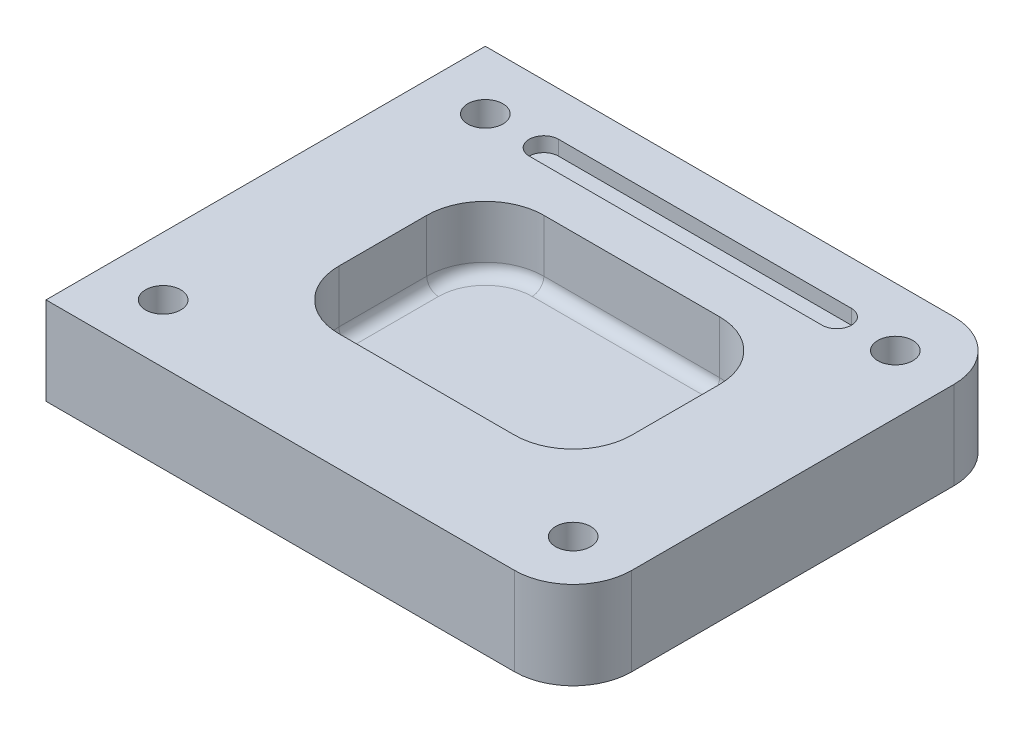
SolidWorks part; units mm, degrees
ref_plane "Front Plane" through (0, 0, 0) normal (0, 0, 1) x (1, 0, 0)
ref_plane "Top Plane" through (0, 0, 0) normal (0, 1, 0) x (1, 0, 0)
ref_plane "Right Plane" through (0, 0, 0) normal (1, 0, 0) x (0, 0, -1)
sketch "Sketch1" plane through (0, 0, 0) normal (0, 1, 0) x (1, 0, 0)
  line L1 (-90, -75) -> (90, -75)
  line L2 (-90, -75) -> (-90, 75)
  line L3 (-90, 75) -> (90, 75)
  line L4 (90, -75) -> (90, 75)
  line L5 (-90, -75) -> (90, 75) construction
  line L6 (-90, 75) -> (90, -75) construction
  point P0 (0, 0)
  dimension "D1" = 180
  dimension "D2" = 150
extrude "Boss-Extrude1" add sketch "Sketch1" along normal blind 30
sketch "Sketch2" plane through (0, 30, 0) normal (0, 1, 0) x (1, 0, 0)
  line L8 (70, -55) -> (70, 55)
  line L9 (70, 55) -> (-70, 55)
  line L10 (-70, 55) -> (-70, -55)
  line L11 (-70, -55) -> (70, -55)
  line L12 (70, -55) -> (70, 55) construction
  line L13 (70, 55) -> (-70, 55) construction
  line L14 (-70, 55) -> (-70, -55) construction
  line L15 (-70, -55) -> (70, -55) construction
  dimension "D1" = 20
hole_wizard "Ø16.0mm Dowel Hole1" positions "3DSketch2" profile "Sketch4" hole size "Ø16.0" standard "ANSI Metric"
sketch3d "3DSketch2"
  point P0 (-70, 30, 55)
  point P3 (-70, 30, -55)
  point P6 (70, 30, -55)
  point P9 (70, 30, 55)
sketch "Sketch4" plane through (-70, 30, 55) normal (1, 0, 0) x (0, 0, 1)
  line L0 (0, 0) -> (0, 13.6052)
  line L1 (0, 13.6052) -> (6, 10)
  line L2 (6, 10) -> (6, 0)
  line L5 (6, 0) -> (0, 0)
  line L10 (0, 13.6052) -> (-6, 10) construction
  line L11 (0, -6.35) -> (0, 107.95) construction
  dimension "Hole Dia." = 12
  dimension "Hole Depth" = 10
  dimension "Drill Angle" = 118
sketch "Sketch5" plane through (0, 30, 0) normal (0, 1, 0) x (1, 0, 0)
  line L8 (50, -35) -> (50, 35)
  line L9 (50, 35) -> (-50, 35)
  line L10 (-50, 35) -> (-50, -35)
  line L11 (-50, -35) -> (50, -35)
  line L12 (50, -35) -> (50, 35)
  line L13 (50, 35) -> (-50, 35)
  line L14 (-50, 35) -> (-50, -35)
  line L15 (-50, -35) -> (50, -35)
  dimension "D1" = 40
extrude "Cut-Extrude1" cut sketch "Sketch5" against normal offset from surface (22 mm away) 8 up to face at (0, 0, 0)
fillet "Fillet1" radius 20 4 edges at (50, 19, 35) (-50, 19, 35) (50, 19, -35) (-50, 19, -35)
fillet "Fillet2" radius 20 2 edges at (90, 15, 75) (90, 15, -75)
sketch "Sketch6" plane through (0, 30, 0) normal (0, 1, 0) x (1, 0, 0)
  line L0 (-50, 55) -> (50, 55) construction
  line L1 (-50, 60) -> (50, 60)
  line L2 (-50, 50) -> (50, 50)
  arc A0 (-50, 60) -> (-50, 50) centre (-50, 55) ccw
  arc A1 (50, 50) -> (50, 60) centre (50, 55) ccw
  point P3 (0, 55)
  dimension "D1" = 5
  dimension "D2" = 100
  dimension "D3" = 20
extrude "Cut-Extrude2" cut sketch "Sketch6" against normal blind 5
fillet "Fillet3" radius 4 8 edges at (-50, 8, 0) (-44.1421, 8, 29.1421) (0, 8, 35) (44.1421, 8, 29.1421) (50, 8, 0) (44.1421, 8, -29.1421) (0, 8, -35) (-44.1421, 8, -29.1421)
